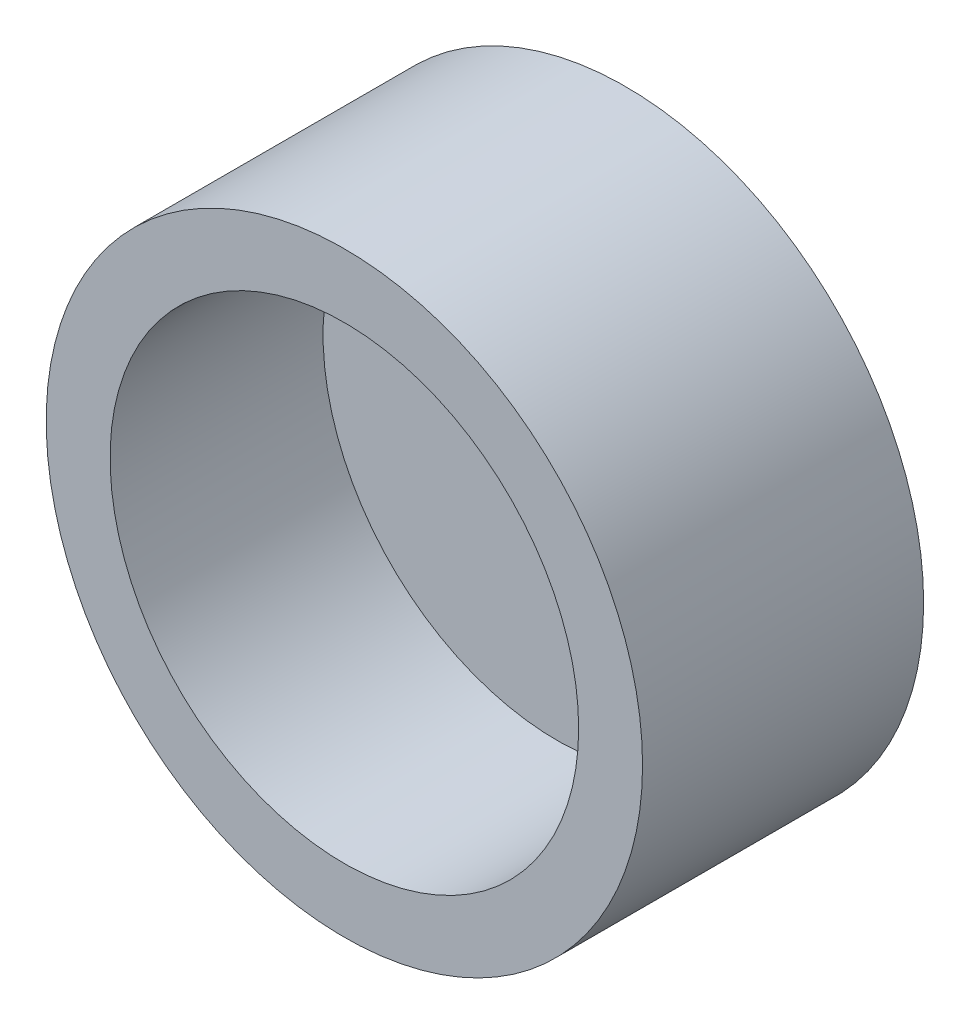
SolidWorks part; units mm, degrees
material "AISI 1020"
ref_plane "Front Plane" through (0, 0, 0) normal (0, 0, 1) x (1, 0, 0)
ref_plane "Top Plane" through (0, 0, 0) normal (0, 1, 0) x (1, 0, 0)
ref_plane "Right Plane" through (0, 0, 0) normal (1, 0, 0) x (0, 0, -1)
sketch "Sketch1" plane through (0, 0, 0) normal (0, 0, 1) x (1, 0, 0)
  circle A0 centre (0, 0) radius 88.9
  dimension "D1" = 177.8
extrude "Boss-Extrude1" add sketch "Sketch1" along normal blind 83.8
sketch "Sketch2" plane through (0, 0, 0) normal (0, 0, -1) x (-1, 0, 0)
  line L1 (19.05, -50) -> (-19.05, -50) construction
  line L2 (19.05, -50) -> (19.05, 50) construction
  line L3 (19.05, 50) -> (-19.05, 50) construction
  line L4 (-19.05, -50) -> (-19.05, 50) construction
  line L5 (19.05, -50) -> (-19.05, 50) construction
  line L6 (19.05, 50) -> (-19.05, -50) construction
  line L7 (19.05, 50) -> (-19.05, 50)
  line L8 (19.05, 50) -> (19.05, 35)
  line L9 (19.05, 35) -> (-19.05, 35)
  line L10 (-19.05, 50) -> (-19.05, 35)
  line L11 (19.05, -50) -> (-19.05, -50)
  line L12 (19.05, -50) -> (19.05, -35)
  line L13 (19.05, -35) -> (-19.05, -35)
  line L14 (-19.05, -50) -> (-19.05, -35)
  point P0 (0, 0)
  point P1 (0, 0)
  dimension "D1" = 100
  dimension "D2" = 38.1
  dimension "D3" = 15
  dimension "D4" = 15
extrude "Boss-Extrude2" add sketch "Sketch2" along normal blind 10
sketch "Sketch4" plane through (19.05, 0, 0) normal (1, 0, 0) x (0, 0, -1)
  line L0 (10, 50) -> (10, 35) construction
  circle A0 centre (10, 42.5) radius 2.5
  point P0 (10, 50)
  point P1 (10, 35)
  point P3 (10, 42.5)
  dimension "D1" = 5
extrude "Cut-Extrude1" cut sketch "Sketch4" against normal through all
sketch "Sketch5" plane through (19.05, 0, 0) normal (1, 0, 0) x (0, 0, -1)
  line L0 (10, -35) -> (10, -50) construction
  circle A0 centre (10, -42.5) radius 2.5
  point P0 (10, -35)
  point P1 (10, -50)
  point P3 (10, -42.5)
  dimension "D1" = 5
extrude "Cut-Extrude2" cut sketch "Sketch5" against normal up to surface (38.1 mm away) up to face at (-19.05, -42.5, -5)
sketch "Sketch6" plane through (0, 0, 83.8) normal (0, 0, 1) x (1, 0, 0)
  circle A0 centre (0, 0) radius 69.85
  point P0 (0, 0)
  dimension "D1" = 139.7
extrude "Cut-Extrude3" cut sketch "Sketch6" against normal blind 63.5
